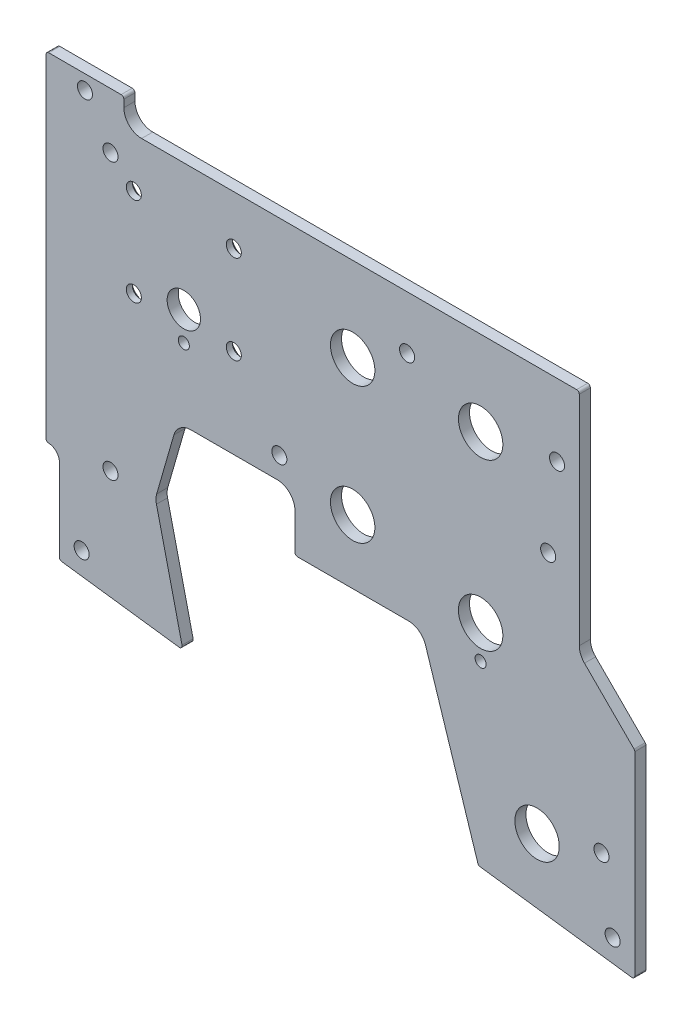
SolidWorks part; units mm, degrees
ref_plane "Front Plane" through (0, 0, 0) normal (0, 0, 1) x (1, 0, 0)
ref_plane "Top Plane" through (0, 0, 0) normal (0, 1, 0) x (1, 0, 0)
ref_plane "Right Plane" through (0, 0, 0) normal (1, 0, 0) x (0, 0, -1)
sketch "Sketch1" plane through (0, 0, 0) normal (0, 0, 1) x (1, 0, 0)
  line L16 (3.81, -91.8845) -> (3.81, -115.4033)
  line L17 (4.4725, -116.1588) -> (38.0231, -120.5758)
  line L18 (38.8645, -119.6465) -> (31.5446, -88.4134)
  line L19 (31.6093, -85.8475) -> (36.5334, -68.7608)
  line L20 (41.4148, -65.0875) -> (66.04, -65.0875)
  line L21 (71.12, -70.1675) -> (71.12, -80.518)
  line L22 (71.882, -81.28) -> (103.6122, -81.28)
  line L23 (108.4484, -84.805) -> (123.4233, -131.3792)
  line L24 (124.0493, -131.9014) -> (167.4135, -137.6104)
  line L25 (168.275, -136.8549) -> (168.275, -81.3036)
  line L26 (168.0518, -80.7647) -> (153.8879, -66.6008)
  line L27 (152.4, -63.0087) -> (152.4, -0.762)
  line L28 (151.638, 0) -> (27.305, 0)
  line L29 (22.225, 5.08) -> (22.225, 7.1755)
  line L30 (21.463, 7.9375) -> (0.762, 7.9375)
  line L31 (0, 7.1755) -> (0, -87.9495)
  line L32 (3.81, -91.8845) -> (3.81, -115.4033)
  line L33 (4.4725, -116.1588) -> (38.0231, -120.5758)
  line L34 (38.8645, -119.6465) -> (31.5446, -88.4134)
  line L35 (31.6093, -85.8475) -> (36.5334, -68.7608)
  line L36 (41.4148, -65.0875) -> (66.04, -65.0875)
  line L37 (71.12, -70.1675) -> (71.12, -80.518)
  line L38 (71.882, -81.28) -> (103.6122, -81.28)
  line L39 (108.4484, -84.805) -> (123.4233, -131.3792)
  line L40 (124.0493, -131.9014) -> (167.4135, -137.6104)
  line L41 (168.275, -136.8549) -> (168.275, -81.3036)
  line L42 (168.0518, -80.7647) -> (153.8879, -66.6008)
  line L43 (152.4, -63.0087) -> (152.4, -0.762)
  line L44 (151.638, 0) -> (27.305, 0)
  line L45 (22.225, 5.08) -> (22.225, 7.1755)
  line L46 (21.463, 7.9375) -> (0.762, 7.9375)
  line L47 (0, 7.1755) -> (0, -87.9495)
  arc A17 (3.81, -91.8845) -> (0.7374, -88.7112) centre (0.635, -91.8845) ccw
  arc A18 (3.81, -115.4033) -> (4.4725, -116.1588) centre (4.572, -115.4033) ccw
  arc A19 (38.0231, -120.5758) -> (38.8645, -119.6465) centre (38.1226, -119.8204) ccw
  arc A20 (31.6093, -85.8475) -> (31.5446, -88.4134) centre (36.4906, -87.2542) ccw
  arc A21 (41.4148, -65.0875) -> (36.5334, -68.7608) centre (41.4148, -70.1675) ccw
  arc A22 (71.12, -70.1675) -> (66.04, -65.0875) centre (66.04, -70.1675) ccw
  arc A23 (71.12, -80.518) -> (71.882, -81.28) centre (71.882, -80.518) ccw
  arc A24 (108.4484, -84.805) -> (103.6122, -81.28) centre (103.6122, -86.36) ccw
  arc A25 (123.4233, -131.3792) -> (124.0493, -131.9014) centre (124.1487, -131.1459) ccw
  arc A26 (167.4135, -137.6104) -> (168.275, -136.8549) centre (167.513, -136.8549) ccw
  arc A27 (168.275, -81.3036) -> (168.0518, -80.7647) centre (167.513, -81.3036) ccw
  arc A28 (152.4, -63.0087) -> (153.8879, -66.6008) centre (157.48, -63.0087) ccw
  arc A29 (152.4, -0.762) -> (151.638, 0) centre (151.638, -0.762) ccw
  arc A30 (22.225, 5.08) -> (27.305, 0) centre (27.305, 5.08) ccw
  arc A31 (22.225, 7.1755) -> (21.463, 7.9375) centre (21.463, 7.1755) ccw
  arc A32 (0.762, 7.9375) -> (0, 7.1755) centre (0.762, 7.1755) ccw
  arc A33 (0, -87.9495) -> (0.7374, -88.7112) centre (0.762, -87.9495) ccw
  arc A34 (3.81, -91.8845) -> (0.7374, -88.7112) centre (0.635, -91.8845) ccw
  arc A35 (3.81, -115.4033) -> (4.4725, -116.1588) centre (4.572, -115.4033) ccw
  arc A36 (38.0231, -120.5758) -> (38.8645, -119.6465) centre (38.1226, -119.8204) ccw
  arc A37 (31.6093, -85.8475) -> (31.5446, -88.4134) centre (36.4906, -87.2542) ccw
  arc A38 (41.4148, -65.0875) -> (36.5334, -68.7608) centre (41.4148, -70.1675) ccw
  arc A39 (71.12, -70.1675) -> (66.04, -65.0875) centre (66.04, -70.1675) ccw
  arc A40 (71.12, -80.518) -> (71.882, -81.28) centre (71.882, -80.518) ccw
  arc A41 (108.4484, -84.805) -> (103.6122, -81.28) centre (103.6122, -86.36) ccw
  arc A42 (123.4233, -131.3792) -> (124.0493, -131.9014) centre (124.1487, -131.1459) ccw
  arc A43 (167.4135, -137.6104) -> (168.275, -136.8549) centre (167.513, -136.8549) ccw
  arc A44 (168.275, -81.3036) -> (168.0518, -80.7647) centre (167.513, -81.3036) ccw
  arc A45 (152.4, -63.0087) -> (153.8879, -66.6008) centre (157.48, -63.0087) ccw
  arc A46 (152.4, -0.762) -> (151.638, 0) centre (151.638, -0.762) ccw
  arc A47 (22.225, 5.08) -> (27.305, 0) centre (27.305, 5.08) ccw
  arc A48 (22.225, 7.1755) -> (21.463, 7.9375) centre (21.463, 7.1755) ccw
  arc A49 (0.762, 7.9375) -> (0, 7.1755) centre (0.762, 7.1755) ccw
  arc A50 (0, -87.9495) -> (0.7374, -88.7112) centre (0.762, -87.9495) ccw
  dimension "D1" = 0
extrude "Boss-Extrude1" add sketch "Sketch1" against normal blind 3.175
hole_wizard "#6 Clearance Hole1" positions "Sketch3" profile "Sketch2" hole size "#6" standard "ANSI Inch" end condition through all
sketch "Sketch3" plane through (0, 0, -3.175) normal (0, 0, -1) x (-1, 0, 0)
  point P0 (-11.1125, 3.81)
  point P3 (-18.415, -7.9375)
  point P6 (-103.1875, -15.24)
  point P9 (-143.51, -44.45)
  point P12 (-158.75, -111.125)
  point P15 (-18.415, -86.741)
  point P18 (-66.675, -58.7375)
  point P21 (-10.16, -110.5028)
  point P25 (-146.05, -20.6375)
  point P28 (-161.925, -130.483)
sketch "Sketch2" plane through (11.1125, 3.81, -3.175) normal (1, 0, 0) x (0, 1, 0)
  line L0 (0, 0) -> (0, 3.175)
  line L1 (0, 3.175) -> (2.1526, 3.175)
  line L2 (2.1526, 3.175) -> (2.1526, 0)
  line L5 (2.1526, 0) -> (0, 0)
  line L11 (0, -6.35) -> (0, 107.95) construction
  dimension "Thru Hole Dia." = 4.3053
  dimension "Thru Hole Depth" = 3.175
sketch "Sketch4" plane through (0, 0, -3.175) normal (0, 0, -1) x (-1, 0, 0)
  circle A0 centre (-140.335, -115.57) radius 6.35
  circle A1 centre (-124.206, -71.4375) radius 6.35
  circle A2 centre (-87.63, -62.992) radius 6.35
  circle A3 centre (-87.63, -24.13) radius 6.35
  circle A4 centre (-124.206, -24.13) radius 6.35
  circle A5 centre (-124.206, -80.9625) radius 1.5875
  circle A6 centre (-39.37, -36.322) radius 4.7625
  dimension "D1" = 12.7
  dimension "D2" = 3.175
  dimension "D4" = 9.525
  dimension "D3" = 9.525
extrude "Cut-Extrude1" cut sketch "Sketch4" against normal through all
hole_wizard "CSK for #6 Flat Head Machine Screw (100)1" positions "Sketch6" profile "Sketch5" countersink size "#6" standard "ANSI Inch" end condition through all
sketch "Sketch6" plane through (0, 0, -3.175) normal (0, 0, -1) x (-1, 0, 0)
  point P0 (-53.6575, -14.097)
  point P2 (-25.0825, -14.097)
  point P4 (-25.0825, -39.497)
  point P6 (-53.6575, -39.497)
sketch "Sketch5" plane through (53.6575, -14.097, -3.175) normal (1, 0, 0) x (0, 1, 0)
  line L0 (0, 0) -> (0, 3.175)
  line L1 (0, 3.175) -> (2.1526, 3.175)
  line L2 (2.1526, 3.175) -> (2.1526, 1.4209)
  line L3 (2.1526, 1.4209) -> (3.846, 0)
  line L5 (3.846, 0) -> (0, 0)
  line L6 (-2.1526, 1.4209) -> (-3.846, 0) construction
  line L11 (0, -6.35) -> (0, 107.95) construction
  dimension "Thru Hole Dia." = 4.3053
  dimension "Thru Hole Depth" = 3.175
  dimension "Near C'Sink Dia." = 7.692
  dimension "Near C'Sink Angle" = 100
hole_wizard "#0 Clearance Hole1" positions "Sketch7" profile "Sketch8" hole size "#0" standard "ANSI Inch" end condition through all
sketch "Sketch7" plane through (0, 0, -9.525) normal (0, 0, -1) x (-1, 0, 0)
  point P0 (-39.37, -44.577)
sketch "Sketch8" plane through (39.37, -44.577, -9.525) normal (1, 0, 0) x (0, 1, 0)
  line L0 (0, 0) -> (0, 9.525)
  line L1 (0, 9.525) -> (0.9271, 9.525)
  line L2 (0.9271, 9.525) -> (0.9271, 0)
  line L3 (0.9271, 0) -> (0, 0)
  line L4 (0, -6.35) -> (0, 107.95) construction
  dimension "Thru Hole Dia." = 1.8542
  dimension "Thru Hole Depth" = 9.525
hole_wizard "1/8 (0.125) Diameter Hole1" positions "Sketch9" profile "Sketch10" hole size "1/8" standard "ANSI Inch" end condition through all
sketch "Sketch9" plane through (0, 0, 0) normal (0, 0, 1) x (1, 0, 0)
  point P0 (39.37, -44.577)
  point P2 (39.37, -44.577)
sketch "Sketch10" plane through (39.37, -44.577, 0) normal (1, 0, 0) x (0, -1, 0)
  line L0 (0, 0) -> (0, 3.175)
  line L1 (0, 3.175) -> (1.5875, 3.175)
  line L2 (1.5875, 3.175) -> (1.5875, 0)
  line L5 (1.5875, 0) -> (0, 0)
  line L11 (0, -6.35) -> (0, 107.95) construction
  dimension "Thru Hole Dia." = 3.175
  dimension "Thru Hole Depth" = 3.175
